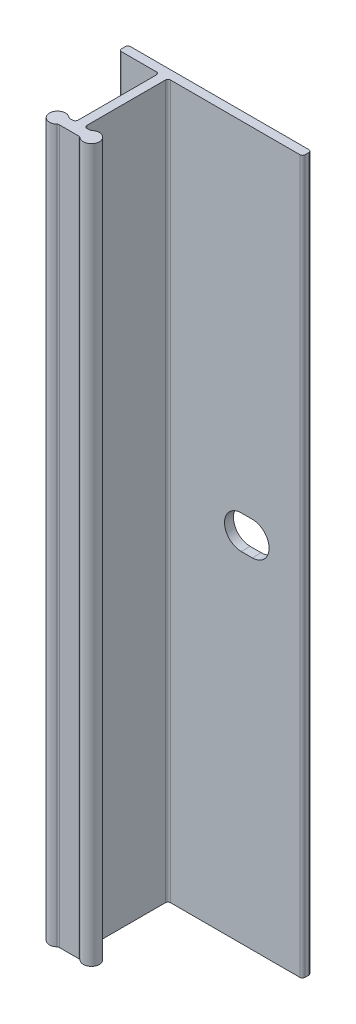
SolidWorks part; units mm, degrees
material "6463-T6"
ref_plane "Front Plane" through (0, 0, 0) normal (0, 0, 1) x (1, 0, 0)
ref_plane "Top Plane" through (0, 0, 0) normal (0, 1, 0) x (1, 0, 0)
ref_plane "Right Plane" through (0, 0, 0) normal (1, 0, 0) x (0, 0, -1)
sketch "Sketch2" plane through (0, 0, 0) normal (0, 1, 0) x (1, 0, 0)
  line L0 (0, 7.209) -> (0, -15.6826) construction
  line L16 (-5.969, 0) -> (19.431, 0)
  line L18 (19.812, -0.381) -> (19.812, -0.889)
  line L19 (19.431, -1.27) -> (1.016, -1.27)
  line L20 (0.635, -1.651) -> (0.635, -12.827)
  line L52 (-0.635, -1.651) -> (-0.635, -12.827)
  line L53 (-8.0148, -13.97) -> (8.0148, -13.97) construction
  line L54 (-1.405, -13.208) -> (-1.016, -13.208)
  line L55 (-1.405, -14.732) -> (1.405, -14.732)
  line L56 (1.016, -13.208) -> (1.405, -13.208)
  line L57 (-1.016, -1.27) -> (-5.969, -1.27)
  line L58 (-6.35, -0.889) -> (-6.35, -0.381)
  arc A11 (19.431, 0) -> (19.812, -0.381) centre (19.431, -0.381) cw
  arc A12 (19.812, -0.889) -> (19.431, -1.27) centre (19.431, -0.889) cw
  arc A19 (1.016, -1.27) -> (0.635, -1.651) centre (1.016, -1.651) ccw
  arc A20 (-1.657, -13.1128) -> (-1.657, -14.8273) centre (-2.413, -13.97) ccw
  arc A21 (1.657, -14.8273) -> (1.657, -13.1128) centre (2.413, -13.97) ccw
  arc A22 (0.635, -12.827) -> (1.016, -13.208) centre (1.016, -12.827) ccw
  arc A23 (-0.635, -12.827) -> (-1.016, -13.208) centre (-1.016, -12.827) cw
  arc A24 (1.405, -14.732) -> (1.657, -14.8273) centre (1.405, -15.113) cw
  arc A25 (1.657, -13.1128) -> (1.405, -13.208) centre (1.405, -12.827) cw
  arc A26 (-1.405, -14.732) -> (-1.657, -14.8273) centre (-1.405, -15.113) ccw
  arc A27 (-1.405, -13.208) -> (-1.657, -13.1128) centre (-1.405, -12.827) cw
  arc A28 (-6.35, -0.381) -> (-5.969, 0) centre (-5.969, -0.381) cw
  arc A29 (-5.969, -1.27) -> (-6.35, -0.889) centre (-5.969, -0.889) cw
  arc A30 (-1.016, -1.27) -> (-0.635, -1.651) centre (-1.016, -1.651) cw
  point P7 (0, -13.97)
  point P16 (19.812, 0)
  point P19 (19.812, -1.27)
  point P22 (0.635, -1.27)
  point P30 (0.635, -13.208)
  point P36 (1.5611, -14.732)
  point P39 (1.5611, -13.208)
  point P42 (-1.5611, -14.732)
  point P45 (-1.5611, -13.208)
  dimension "D7" = 0.381
  dimension "D6" = 2.286
  dimension "D10" = 1.524
  dimension "D11" = 19.812
  dimension "D12" = 6.35
  dimension "D2" = 1.27
  dimension "D3" = 1.27
  dimension "D4" = 0.635
  dimension "D5" = 13.97
  dimension "D8" = 2.413
  dimension "D9" = 2.413
extrude "Boss-Extrude1" add sketch "Sketch2" along normal mid plane 101.6
sketch "Sketch3" plane through (0, 0, 1.27) normal (0, 0, 1) x (1, 0, 0)
  line L0 (0, 0) -> (19.812, 0) construction
  line L1 (19.812, 50.8) -> (19.812, -50.8) construction
  line L2 (11.0808, 0) -> (12.6683, 0) construction
  line L3 (11.0808, 2.3813) -> (12.6683, 2.3813)
  line L4 (11.0808, -2.3813) -> (12.6683, -2.3812)
  arc A0 (11.0808, 2.3813) -> (11.0808, -2.3813) centre (11.0808, 0) ccw
  arc A1 (12.6683, -2.3812) -> (12.6683, 2.3813) centre (12.6683, 0) ccw
  point P7 (11.8745, 0)
  dimension "D1" = 4.7625
  dimension "D2" = 6.35
  dimension "D3" = 7.9375
extrude "Cut-Extrude1" cut sketch "Sketch3" against normal through all
